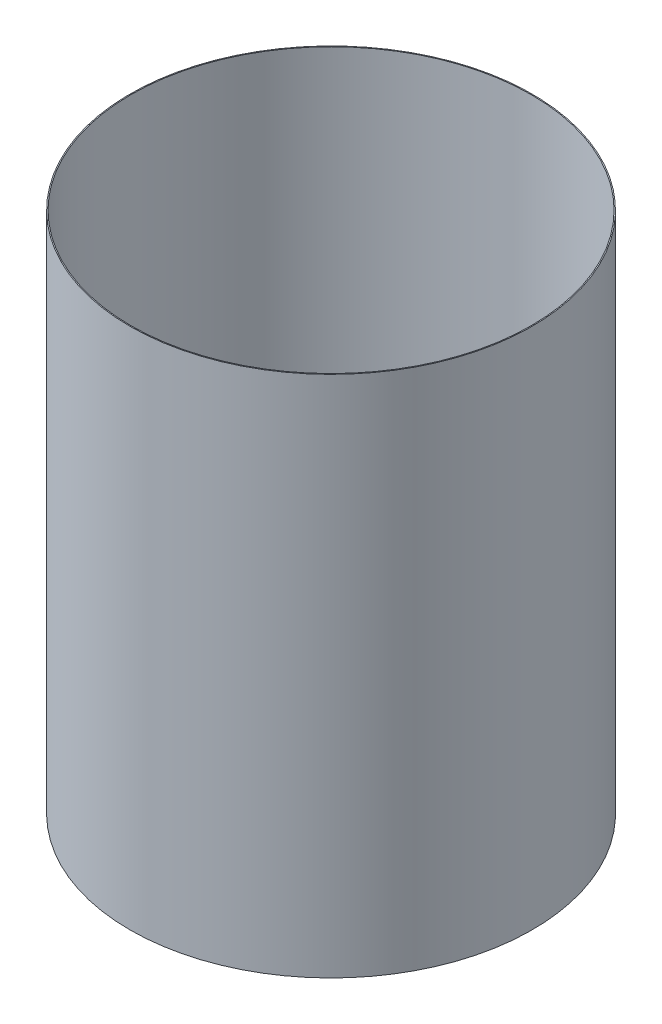
SolidWorks part; units mm, degrees
material "Thornel Mat VMA"
ref_plane "Front Plane" through (0, 0, 0) normal (0, 0, 1) x (1, 0, 0)
ref_plane "Top Plane" through (0, 0, 0) normal (0, 1, 0) x (1, 0, 0)
ref_plane "Right Plane" through (0, 0, 0) normal (1, 0, 0) x (0, 0, -1)
ref_axis "Axis1" through (0, 55, 0) along (0, -1, 0)
sketch "Sketch1" plane through (0, 0, 0) normal (0, 0, 1) x (1, 0, 0)
  line L0 (-51.054, -19.9059) -> (-51.054, -153.2559)
  line L2 (-38.1, -19.9059) -> (0, -19.9059) construction
  line L3 (-38.1, -153.2559) -> (0, -153.2559) construction
revolve "Revolve-Thin1" add sketch "Sketch1" angle 360 about axis through (0, 55, 0) along (0, -1, 0)
equation "\"D3@Revolve-Thin1\"=\"CF THICKNESS@Cryo Tank.Assembly\""
